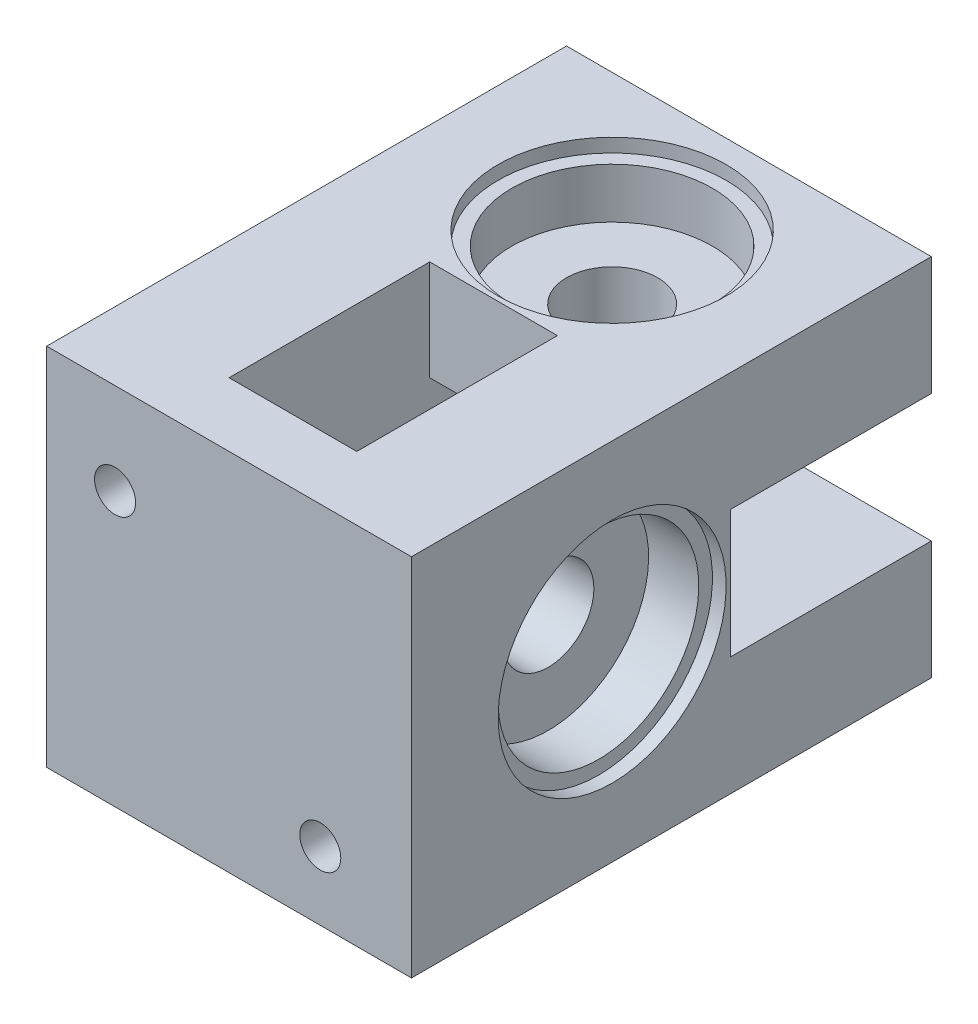
SolidWorks part; units mm, degrees
ref_plane "Plan de face" through (0, 0, 0) normal (0, 0, 1) x (1, 0, 0)
ref_plane "Plan de dessus" through (0, 0, 0) normal (0, 1, 0) x (1, 0, 0)
ref_plane "Plan de droite" through (0, 0, 0) normal (1, 0, 0) x (0, 0, -1)
sketch "Esquisse1" plane through (0, 0, 0) normal (0, 0, 1) x (1, 0, 0)
  line L1 (-40, 40) -> (0, 40)
  line L2 (-40, 40) -> (-40, 0)
  line L3 (-40, 0) -> (0, 0)
  line L4 (0, 40) -> (0, 0)
  dimension "D1" = 40
  dimension "D2" = 40
extrude "Boss.-Extru.1" add sketch "Esquisse1" along normal blind 50
sketch "Esquisse2" plane through (0, 40, 0) normal (0, 1, 0) x (1, 0, 0)
  line L0 (0, 0) -> (-40, 0) construction
  line L1 (-40, -50) -> (-40, 0) construction
  circle A0 centre (-20, -15) radius 5
  dimension "D1" = 10
  dimension "D2" = 15
  dimension "D3" = 20
extrude "Enlèv. mat.-Extru.1" cut sketch "Esquisse2" against normal through all
sketch "Esquisse3" plane through (-40, 0, 0) normal (-1, 0, 0) x (0, 0, 1)
  line L0 (50, 40) -> (50, 0) construction
  line L1 (50, 40) -> (0, 40) construction
  circle A0 centre (35, 20) radius 5
  dimension "D1" = 10
  dimension "D2" = 15
  dimension "D3" = 20
extrude "Enlèv. mat.-Extru.2" cut sketch "Esquisse3" against normal through all
sketch "Esquisse4" plane through (-40, 0, 0) normal (-1, 0, 0) x (0, 0, 1)
  line L1 (25, 27) -> (5, 27)
  line L2 (25, 27) -> (25, 13)
  line L3 (25, 13) -> (5, 13)
  line L4 (5, 27) -> (5, 13)
  line L5 (0, 40) -> (0, 0) construction
  line L6 (50, 0) -> (0, 0) construction
  line L7 (50, 40) -> (0, 40) construction
  dimension "D1" = 14
  dimension "D2" = 20
  dimension "D3" = 5
  dimension "D4" = 13
  dimension "D5" = 13
extrude "Enlèv. mat.-Extru.3" cut sketch "Esquisse4" against normal blind 29
sketch "Esquisse5" plane through (0, 0, 0) normal (0, -1, 0) x (1, 0, 0)
  line L0 (-40, 50) -> (0, 50) construction
  line L1 (-13, 25) -> (-27, 25)
  line L2 (-13, 25) -> (-13, 45)
  line L3 (-13, 45) -> (-27, 45)
  line L4 (-27, 25) -> (-27, 45)
  line L5 (-40, 50) -> (-40, 0) construction
  dimension "D1" = 20
  dimension "D2" = 5
  dimension "D3" = 14
  dimension "D4" = 13
extrude "Enlèv. mat.-Extru.4" cut sketch "Esquisse5" against normal blind 29
sketch "Esquisse6" plane through (0, 0, 0) normal (1, 0, 0) x (0, 0, -1)
  line L0 (0, 0) -> (0, 40) construction
  line L1 (0, 27) -> (-22, 27)
  line L2 (0, 27) -> (0, 13)
  line L3 (0, 13) -> (-22, 13)
  line L4 (-22, 27) -> (-22, 13)
  line L5 (-50, 0) -> (0, 0) construction
  dimension "D1" = 14
  dimension "D2" = 22
  dimension "D3" = 13
extrude "Enlèv. mat.-Extru.5" cut sketch "Esquisse6" against normal blind 24
sketch "Esquisse7" plane through (0, 40, 0) normal (0, 1, 0) x (1, 0, 0)
  line L0 (0, -50) -> (-40, -50) construction
  line L1 (-27, -50) -> (-13, -50)
  line L2 (-27, -50) -> (-27, -28)
  line L3 (-27, -28) -> (-13, -28)
  line L4 (-13, -50) -> (-13, -28)
  line L5 (-40, -50) -> (-40, 0) construction
  dimension "D1" = 14
  dimension "D2" = 22
  dimension "D3" = 13
extrude "Enlèv. mat.-Extru.6" cut sketch "Esquisse7" against normal blind 24
sketch "Esquisse8" plane through (0, 0, 0) normal (1, 0, 0) x (0, 0, -1)
  circle A0 centre (-35, 20) radius 11
  dimension "D1" = 22
extrude "Enlèv. mat.-Extru.7" cut sketch "Esquisse8" against normal blind 7
sketch "Esquisse9" plane through (0, 0, 0) normal (1, 0, 0) x (0, 0, -1)
  circle A0 centre (-35, 20) radius 12.5
  dimension "D1" = 25
extrude "Enlèv. mat.-Extru.8" cut sketch "Esquisse9" against normal blind 1.5
sketch "Esquisse10" plane through (0, 40, 0) normal (0, 1, 0) x (1, 0, 0)
  circle A0 centre (-20, -15) radius 11
  dimension "D1" = 22
extrude "Enlèv. mat.-Extru.9" cut sketch "Esquisse10" against normal blind 7
sketch "Esquisse11" plane through (0, 40, 0) normal (0, 1, 0) x (1, 0, 0)
  circle A0 centre (-20, -15) radius 12.5
  dimension "D1" = 25
extrude "Enlèv. mat.-Extru.10" cut sketch "Esquisse11" against normal blind 1.5
sketch "Esquisse12" plane through (0, 0, 50) normal (0, 0, 1) x (1, 0, 0)
  line L1 (0, 40) -> (-40, 40)
  line L2 (0, 40) -> (0, 0)
  line L3 (0, 0) -> (-40, 0)
  line L4 (-40, 40) -> (-40, 0)
extrude "Boss.-Extru.2" add sketch "Esquisse12" along normal blind 7
sketch "Esquisse13" plane through (0, 0, 57) normal (0, 0, 1) x (1, 0, 0)
  line L0 (0, 0) -> (0, 40) construction
  line L1 (0, 40) -> (-40, 40) construction
  circle A0 centre (-32.5, 30) radius 2.25
  circle A1 centre (-10, 7.5) radius 2.25
  dimension "D1" = 4.5
  dimension "D2" = 32.5
  dimension "D3" = 4.5
  dimension "D4" = 32.5
  dimension "D5" = 10
  dimension "D6" = 10
extrude "Enlèv. mat.-Extru.11" cut sketch "Esquisse13" against normal blind 15
sketch "Esquisse14" plane through (0, 0, 0) normal (0, -1, 0) x (1, 0, 0)
  line L0 (-40, 57) -> (0, 57) construction
  line L1 (-6.25, 49.5) -> (-13.75, 49.5)
  line L2 (-6.25, 49.5) -> (-6.25, 53)
  line L3 (-6.25, 53) -> (-13.75, 53)
  line L4 (-13.75, 49.5) -> (-13.75, 53)
  line L5 (0, 57) -> (0, 0) construction
  dimension "D1" = 7.5
  dimension "D2" = 3.5
  dimension "D3" = 4
  dimension "D4" = 6.25
extrude "Enlèv. mat.-Extru.12" cut sketch "Esquisse14" against normal blind 12
sketch "Esquisse15" plane through (-40, 0, 0) normal (-1, 0, 0) x (0, 0, 1)
  line L0 (57, 40) -> (57, 0) construction
  line L1 (49.5, 26.25) -> (53, 26.25)
  line L2 (49.5, 26.25) -> (49.5, 33.75)
  line L3 (49.5, 33.75) -> (53, 33.75)
  line L4 (53, 26.25) -> (53, 33.75)
  line L5 (57, 40) -> (0, 40) construction
  dimension "D1" = 7.5
  dimension "D2" = 3.5
  dimension "D3" = 4
  dimension "D4" = 6.25
extrude "Enlèv. mat.-Extru.13" cut sketch "Esquisse15" against normal blind 12
